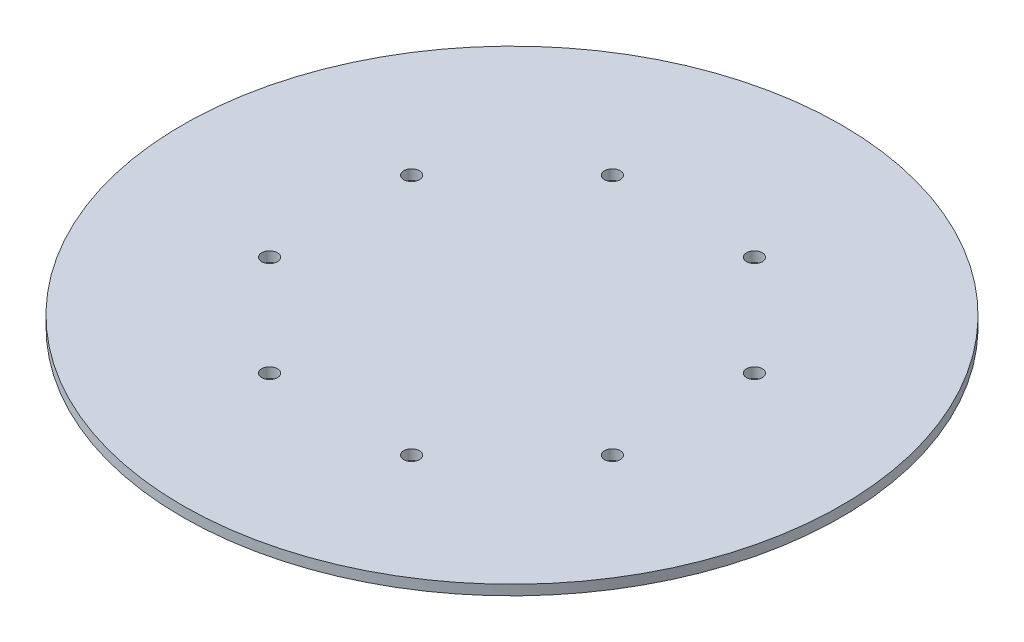
SolidWorks part; units mm, degrees
ref_plane "Front Plane" through (0, 0, 0) normal (0, 0, 1) x (1, 0, 0)
ref_plane "Top Plane" through (0, 0, 0) normal (0, 1, 0) x (1, 0, 0)
ref_plane "Right Plane" through (0, 0, 0) normal (1, 0, 0) x (0, 0, -1)
sketch "Sketch1" plane through (0, 0, 0) normal (0, 1, 0) x (1, 0, 0)
  line L0 (0, 0) -> (22.6249, -54.6215) construction
  line L1 (0, 0) -> (-22.6249, -54.6215) construction
  line L2 (0, 0) -> (-54.6215, -22.6249) construction
  line L3 (0, 0) -> (-54.6215, 22.6249) construction
  line L4 (0, 0) -> (-22.6249, 54.6215) construction
  line L5 (0, 0) -> (22.6249, 54.6215) construction
  line L6 (0, 0) -> (54.6215, 22.6249) construction
  line L7 (0, 0) -> (54.6215, -22.6249) construction
  line L8 (-48.5037, -20.0909) -> (-48.5037, 20.0909) construction
  line L9 (-48.5037, 20.0909) -> (-20.0909, 48.5037) construction
  line L10 (-20.0909, 48.5037) -> (20.0909, 48.5037) construction
  line L11 (20.0909, 48.5037) -> (48.5037, 20.0909) construction
  line L12 (48.5037, 20.0909) -> (48.5037, -20.0909) construction
  line L13 (48.5037, -20.0909) -> (20.0909, -48.5037) construction
  line L14 (20.0909, -48.5037) -> (-20.0909, -48.5037) construction
  line L15 (-20.0909, -48.5037) -> (-48.5037, -20.0909) construction
  line L16 (0, 0) -> (-48.5037, 0) construction
  line L17 (-24.2518, -10.0454) -> (-48.5037, 20.0909) construction
  line L18 (-24.2518, 10.0454) -> (-48.5037, -20.0909) construction
  circle A0 centre (0, 0) radius 52.5
  circle A1 centre (11.3125, -27.3107) radius 1.25
  circle A2 centre (-11.3125, -27.3107) radius 1.25
  circle A3 centre (-27.3107, -11.3125) radius 1.25
  circle A4 centre (-27.3107, 11.3125) radius 1.25
  circle A5 centre (-11.3125, 27.3107) radius 1.25
  circle A6 centre (11.3125, 27.3107) radius 1.25
  circle A7 centre (27.3107, 11.3125) radius 1.25
  circle A8 centre (27.3107, -11.3125) radius 1.25
  circle A9 centre (0, 0) radius 10
  circle A10 centre (-32.3358, 0) radius 1
  circle A11 centre (-22.8649, 22.8649) radius 1
  circle A12 centre (0, 32.3358) radius 1
  circle A13 centre (22.8649, 22.8649) radius 1
  circle A14 centre (32.3358, 0) radius 1
  circle A15 centre (22.8649, -22.8649) radius 1
  circle A16 centre (0, -32.3358) radius 1
  circle A17 centre (-22.8649, -22.8649) radius 1
  point P2 (22.6249, -54.6215)
  point P20 (0, 0)
  point P31 (0, 0)
  point P33 (-24.2518, -10.0454)
  point P48 (0, 0)
  point P49 (-24.2518, 10.0454)
  point P52 (-10.0454, 24.2518)
  point P53 (10.0454, 24.2518)
  point P54 (24.2518, 10.0454)
  point P55 (24.2518, -10.0454)
  point P56 (10.0454, -24.2518)
  point P57 (-10.0454, -24.2518)
  point P58 (0, 0)
  point P61 (0, 0)
  point P62 (0, 0)
  point P76 (0, 0)
  dimension "D1" = 2.5
  dimension "D2" = 20
  dimension "D8" = 8
  dimension "D9" = 2
  dimension "D5" = 52.5
  dimension "D6" = 26.25
  dimension "D7" = 8
  dimension "D3" = 8
  dimension "D4" = 8
extrude "Boss-Extrude1" add sketch "Sketch1" along normal blind 1.6 contours A0 A17 A16 A15 A14 A13 A12 A11 A10 A9 A8 A7 A6 A5 A4 A3 A2 A1 | A10 | A11 | A12 | A14 | A15 | A16
